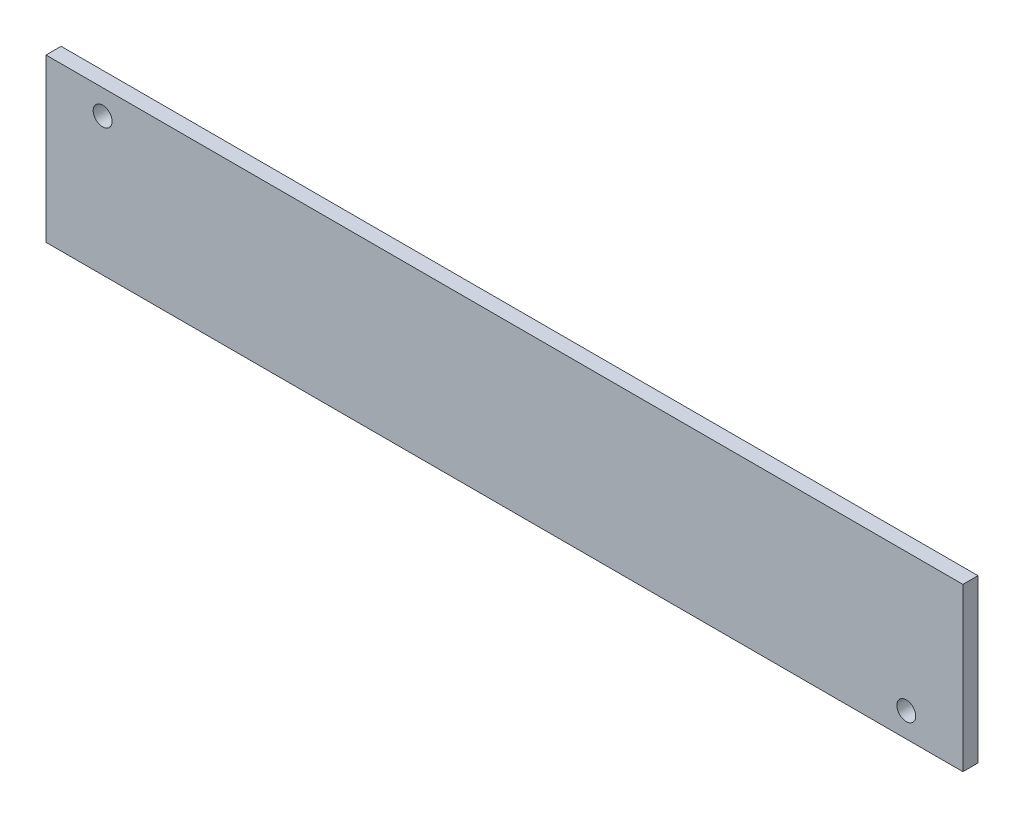
SolidWorks part; units mm, degrees
ref_plane "Front Plane" through (0, 0, 0) normal (0, 0, 1) x (1, 0, 0)
ref_plane "Top Plane" through (0, 0, 0) normal (0, 1, 0) x (1, 0, 0)
ref_plane "Right Plane" through (0, 0, 0) normal (1, 0, 0) x (0, 0, -1)
sketch "Sketch1" plane through (0, 0, 0) normal (0, 0, 1) x (1, 0, 0)
  line L0 (-60.75, -10.75) -> (60.75, 10.75) construction
  line L1 (-60.75, 10.75) -> (60.75, 10.75)
  line L2 (-60.75, 10.75) -> (-60.75, -10.75)
  line L3 (-60.75, -10.75) -> (60.75, -10.75)
  line L4 (60.75, 10.75) -> (60.75, -10.75)
  point P4 (0, 0)
  dimension "D1" = 121.5
  dimension "D2" = 21.5
extrude "Boss-Extrude1" add sketch "Sketch1" along normal blind 2
sketch "Sketch2" plane through (0, 0, 2) normal (0, 0, 1) x (1, 0, 0)
  circle A0 centre (-53.25, 7.5) radius 1.25
  circle A1 centre (53.25, -7.5) radius 1.25
  dimension "D1" = 2.5
extrude "Cut-Extrude1" cut sketch "Sketch2" against normal through all
